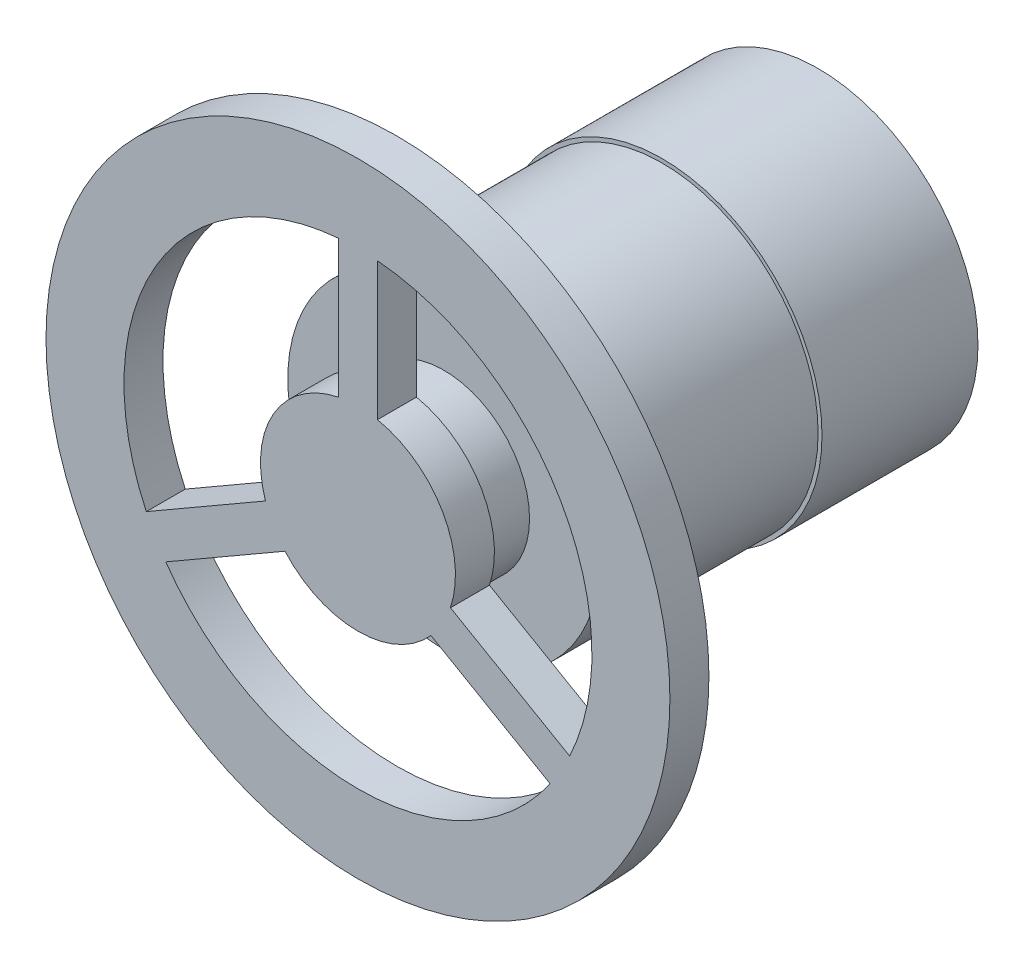
SolidWorks part; units mm, degrees
ref_plane "前视基准面" through (0, 0, 0) normal (0, 0, 1) x (1, 0, 0)
ref_plane "上视基准面" through (0, 0, 0) normal (0, 1, 0) x (1, 0, 0)
ref_plane "右视基准面" through (0, 0, 0) normal (1, 0, 0) x (0, 0, -1)
sketch "草图1" plane through (0, 0, 0) normal (0, 0, 1) x (1, 0, 0)
  circle A0 centre (0, 0) radius 20.5
extrude "凸台-拉伸1" add sketch "草图1" along normal blind 20
sketch "草图4" plane through (0, 0, 20) normal (0, 0, 1) x (1, 0, 0)
  circle A0 centre (0, 0) radius 20
extrude "凸台-拉伸4" add sketch "草图4" along normal blind 28
sketch "草图2" plane through (0, 0, 48) normal (0, 0, 1) x (1, 0, 0)
  circle A0 centre (0, 0) radius 11
extrude "凸台-拉伸2" add sketch "草图2" along normal blind 6
sketch "草图3" plane through (0, 0, 54) normal (0, 0, 1) x (1, 0, 0)
  line L0 (-2.5, 12.2474) -> (-2.5, 29.8957)
  line L5 (11.8566, -3.9587) -> (27.1404, -12.7828)
  line L6 (9.3566, -8.2888) -> (24.6404, -17.1129)
  line L7 (-9.3566, -8.2888) -> (-24.6404, -17.1129)
  line L8 (-11.8566, -3.9587) -> (-27.1404, -12.7828)
  line L9 (2.5, 12.2474) -> (2.5, 29.8957)
  circle A0 centre (0, 0) radius 40
  arc A1 (-2.5, 29.8957) -> (-27.1404, -12.7828) centre (0, 0) ccw
  arc A2 (-2.5, 12.2474) -> (-11.8566, -3.9587) centre (0, 0) ccw
  arc A3 (-9.3566, -8.2888) -> (9.3566, -8.2888) centre (0, 0) ccw
  arc A4 (-24.6404, -17.1129) -> (24.6404, -17.1129) centre (0, 0) ccw
  arc A5 (11.8566, -3.9587) -> (2.5, 12.2474) centre (0, 0) ccw
  arc A6 (27.1404, -12.7828) -> (2.5, 29.8957) centre (0, 0) ccw
  point P19 (0, 0)
  dimension "D1" = 3
extrude "凸台-拉伸3" add sketch "草图3" along normal blind 5
